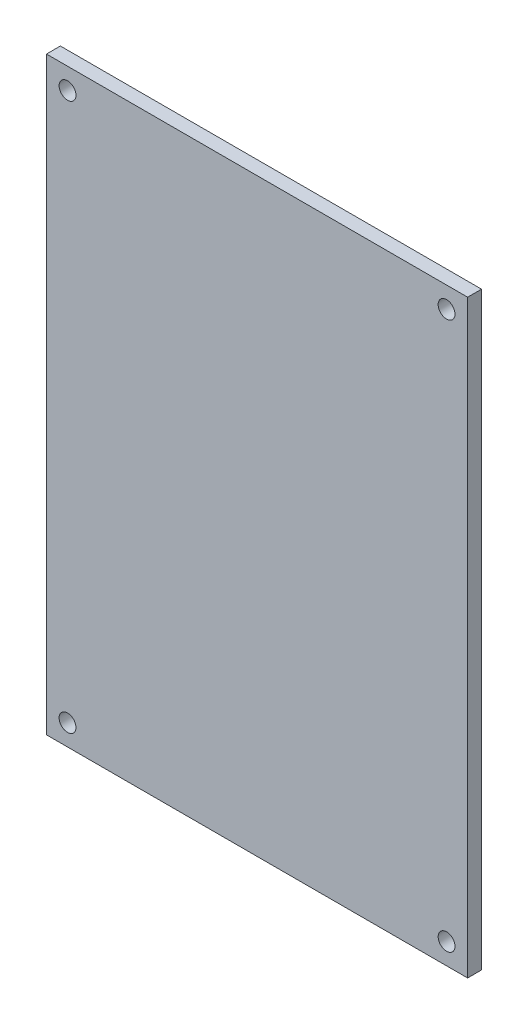
SolidWorks part; units mm, degrees
ref_plane "前视基准面" through (0, 0, 0) normal (0, 0, 1) x (1, 0, 0)
ref_plane "上视基准面" through (0, 0, 0) normal (0, 1, 0) x (1, 0, 0)
ref_plane "右视基准面" through (0, 0, 0) normal (1, 0, 0) x (0, 0, -1)
sketch "草图1" plane through (0, 0, 0) normal (0, 0, 1) x (1, 0, 0)
  line L1 (-25, 35) -> (25, 35)
  line L2 (-25, 35) -> (-25, -35)
  line L3 (-25, -35) -> (25, -35)
  line L4 (25, 35) -> (25, -35)
  line L5 (-25, 35) -> (25, -35) construction
  line L6 (-25, -35) -> (25, 35) construction
  line L7 (-22.5, 32.5) -> (22.5, 32.5) construction
  line L8 (-22.5, 32.5) -> (-22.5, -32.5) construction
  line L9 (-22.5, -32.5) -> (22.5, -32.5) construction
  line L10 (22.5, 32.5) -> (22.5, -32.5) construction
  line L11 (-22.5, 32.5) -> (22.5, -32.5) construction
  line L12 (-22.5, -32.5) -> (22.5, 32.5) construction
  circle A0 centre (-22.5, 32.5) radius 1
  circle A1 centre (22.5, 32.5) radius 1
  circle A2 centre (22.5, -32.5) radius 1
  circle A3 centre (-22.5, -32.5) radius 1
  point P0 (0, 0)
  point P5 (0, 0)
  dimension "D1" = 70
  dimension "D2" = 50
  dimension "D3" = 65
  dimension "D4" = 45
extrude "凸台-拉伸1" add sketch "草图1" along normal blind 1.65
